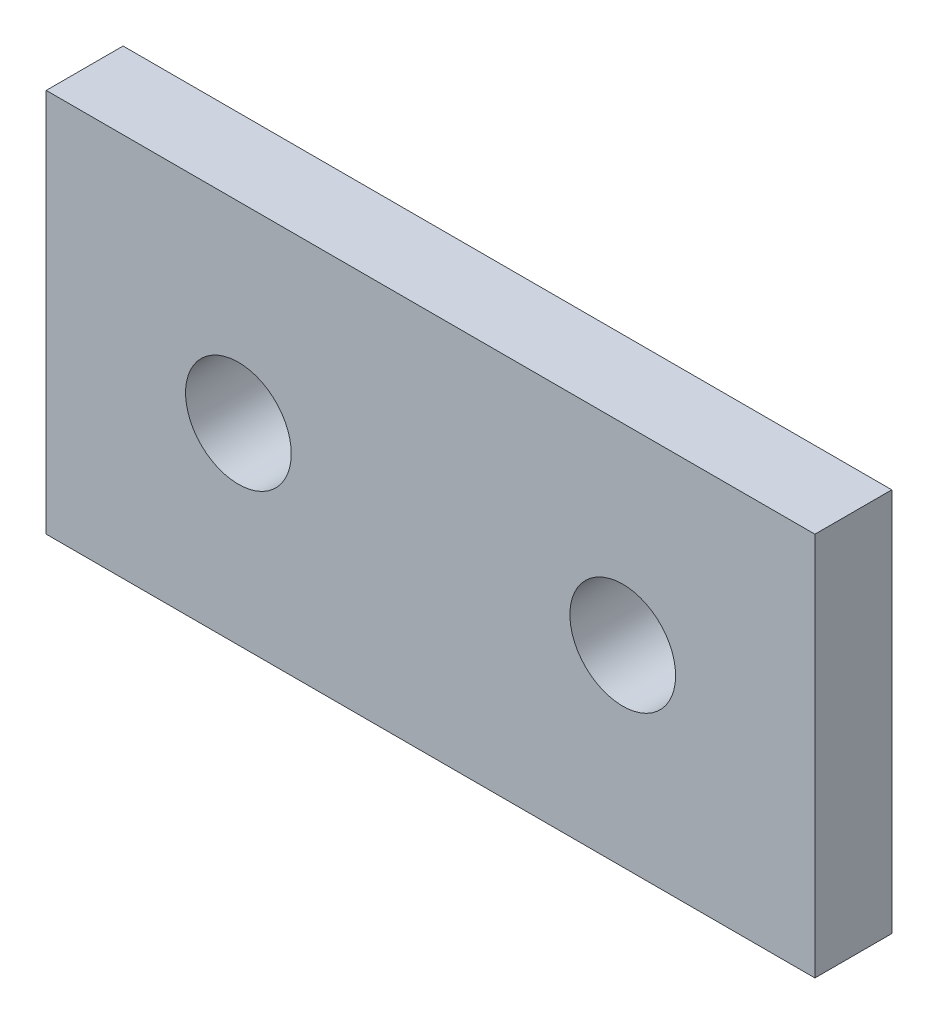
SolidWorks part; units mm, degrees
material "6063-T5"
ref_plane "Front Plane" through (0, 0, 0) normal (0, 0, 1) x (1, 0, 0)
ref_plane "Top Plane" through (0, 0, 0) normal (0, 1, 0) x (1, 0, 0)
ref_plane "Right Plane" through (0, 0, 0) normal (1, 0, 0) x (0, 0, -1)
sketch "Sketch1" plane through (0, 0, 0) normal (0, 0, 1) x (1, 0, 0)
  line L1 (-20, -10) -> (20, -10)
  line L2 (-20, -10) -> (-20, 10)
  line L3 (-20, 10) -> (20, 10)
  line L4 (20, -10) -> (20, 10)
  line L5 (-20, -10) -> (20, 10) construction
  line L6 (-20, 10) -> (20, -10) construction
  circle A0 centre (-10, 0) radius 2.75
  circle A1 centre (10, 0) radius 2.75
  point P0 (0, 0)
  dimension "D3" = 10
  dimension "D5" = 5.5
  dimension "D1" = 40
  dimension "D2" = 20
  dimension "D4" = 20
  dimension "D6" = 10
extrude "Boss-Extrude1" add sketch "Sketch1" along normal mid plane 4
